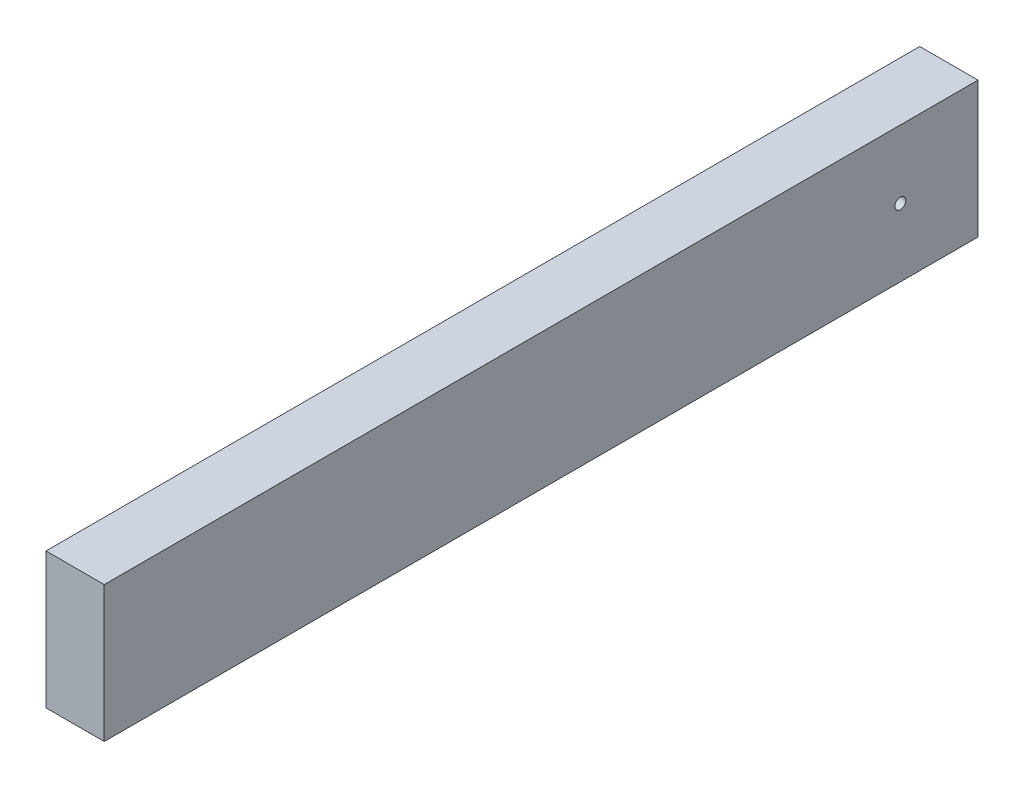
SolidWorks part; units mm, degrees
material "Pine"
ref_plane "Front Plane" through (0, 0, 0) normal (0, 0, 1) x (1, 0, 0)
ref_plane "Top Plane" through (0, 0, 0) normal (0, 1, 0) x (1, 0, 0)
ref_plane "Right Plane" through (0, 0, 0) normal (1, 0, 0) x (0, 0, -1)
sketch "Sketch1" plane through (0, 0, 0) normal (0, 0, 1) x (1, 0, 0)
  line L1 (-19.05, -44.45) -> (19.05, -44.45)
  line L2 (-19.05, -44.45) -> (-19.05, 44.45)
  line L3 (-19.05, 44.45) -> (19.05, 44.45)
  line L4 (19.05, -44.45) -> (19.05, 44.45)
  line L5 (-19.05, -44.45) -> (19.05, 44.45) construction
  line L6 (-19.05, 44.45) -> (19.05, -44.45) construction
  point P0 (0, 0)
  dimension "D1" = 88.9
  dimension "D2" = 38.1
extrude "Boss-Extrude1" add sketch "Sketch1" along normal blind 571.5
sketch "Sketch2" plane through (19.05, 0, 0) normal (1, 0, 0) x (0, 0, -1)
  line L0 (0, -44.45) -> (0, 44.45) construction
  point P0 (-50.8, 0)
  dimension "D1" = 50.8
hole_wizard "9/32 (0.28125) Diameter Hole1" positions "Sketch4" profile "Sketch5" hole size "9/32" standard "ANSI Inch" end condition through all
sketch "Sketch4" plane through (19.05, 0, 0) normal (1, 0, 0) x (0, 0, -1)
  point P0 (-50.8, 0)
sketch "Sketch5" plane through (19.05, 0, 50.8) normal (0, 1, 0) x (0, 0, -1)
  line L0 (0, 0) -> (0, 38.1)
  line L1 (0, 38.1) -> (3.5719, 38.1)
  line L2 (3.5719, 38.1) -> (3.5719, 0)
  line L5 (3.5719, 0) -> (0, 0)
  line L11 (0, -6.35) -> (0, 107.95) construction
  dimension "Thru Hole Dia." = 7.1437
  dimension "Thru Hole Depth" = 38.1
